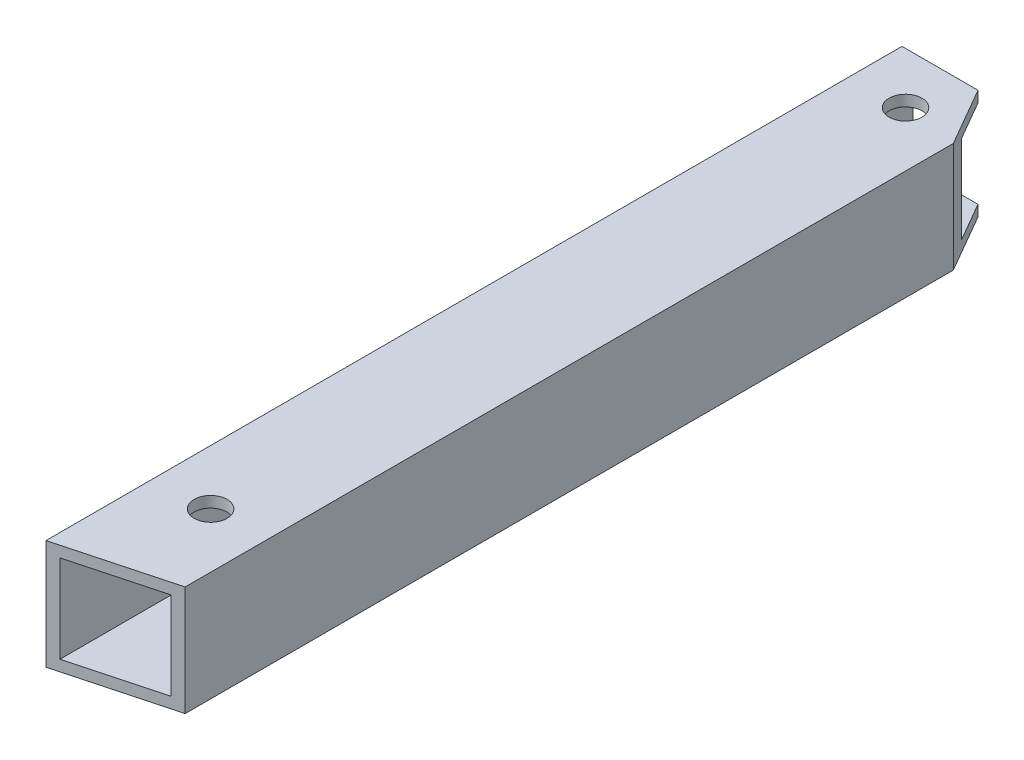
SolidWorks part; units mm, degrees
material "6063-O"
ref_plane "前视基准面" through (0, 0, 0) normal (0, 0, 1) x (1, 0, 0)
ref_plane "上视基准面" through (0, 0, 0) normal (0, 1, 0) x (1, 0, 0)
ref_plane "右视基准面" through (0, 0, 0) normal (1, 0, 0) x (0, 0, -1)
other "Configuration Table"
sketch "草图1" plane through (0, 0, 0) normal (0, 0, 1) x (1, 0, 0)
  line L1 (-5, 5) -> (5, 5)
  line L2 (-5, 5) -> (-5, -5)
  line L3 (-5, -5) -> (5, -5)
  line L4 (5, 5) -> (5, -5)
  line L5 (-5, 5) -> (5, -5) construction
  line L6 (-5, -5) -> (5, 5) construction
  point P4 (0, 0)
  dimension "D1" = 10
  dimension "D2" = 10
extrude "拉伸-薄壁1" add sketch "草图1" along normal blind 90 thin
sketch "草图2" plane through (0, -5, 0) normal (0, -1, 0) x (1, 0, 0)
  line L0 (-5, 0) -> (5, 17.3205)
  line L1 (5, 90) -> (5, 0) construction
  line L2 (5, 17.3205) -> (5, 0)
  line L3 (5, 0) -> (-5, 0)
  line L4 (-5, 90) -> (5, 87.3205)
  line L5 (5, 87.3205) -> (5, 90)
  line L6 (5, 90) -> (-5, 90)
  line L7 (0, 90) -> (0, 0) construction
  line L8 (0, 80) -> (-5, 80) construction
  line L9 (0, 80) -> (30.891, 62.1651) construction
  line L10 (30.891, 62.1651) -> (5, 17.3205) construction
  line L11 (-5, 90) -> (-5, 0) construction
  line L12 (-5, 90) -> (13.4089, 121.8852) construction
  line L13 (13.4089, 121.8852) -> (56.7102, 96.8852) construction
  line L14 (56.7102, 96.8852) -> (-8.5737, -16.1898) construction
  line L15 (0, 90) -> (17.1589, 119.7201) construction
  line L16 (2.75, 94.7631) -> (-1, 96.9282) construction
  line L17 (-5, 19.5633) -> (7.8013, 12.1725) construction
  line L18 (1.9282, 12) -> (-5, 12)
  circle A0 centre (0, 80) radius 1.5
  circle A1 centre (0, 16.6765) radius 1.5
  circle A2 centre (0, 70) radius 1.5 construction
  circle A3 centre (2.75, 94.7631) radius 1.5 construction
  point P35 (0, 8.6603)
  point P36 (0, 0)
  point P37 (1.4842, 11.231)
  line M5 (-5, 0) -> (5, 0)
  line M6 (5, 0) -> (5, 90)
  line M7 (5, 90) -> (-5, 90)
  line M8 (-5, 90) -> (-5, 0)
  dimension "D3" = 3
  dimension "D5" = 69
  dimension "D6" = 10
  dimension "D7" = 5
  dimension "D9" = 3
  dimension "D1" = 15
  dimension "D2" = 60
  dimension "D4" = 10
  dimension "D8" = 8
  dimension "D10" = 73.3235
  dimension "D11" = 12
extrude "切除-拉伸1" cut sketch "草图2" against normal through all contours L0 M5 M6 | L0 L18 M8 | A1 | L4 M7 M6 | A0
